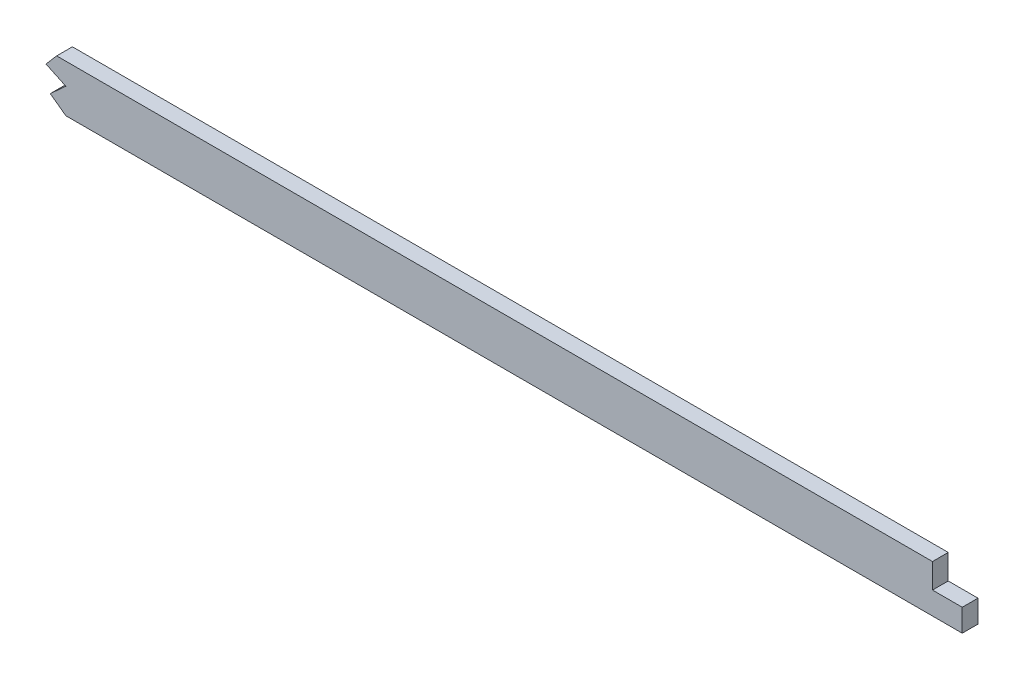
SolidWorks part; units mm, degrees
ref_plane "Front Plane" through (0, 0, 0) normal (0, 0, 1) x (1, 0, 0)
ref_plane "Top Plane" through (0, 0, 0) normal (0, 1, 0) x (1, 0, 0)
ref_plane "Right Plane" through (0, 0, 0) normal (1, 0, 0) x (0, 0, -1)
sketch "Sketch1" plane through (0, 0, 0) normal (0, 0, 1) x (1, 0, 0)
  line L0 (1046.2855, 53.4707) -> (499.61, 53.4707) construction
  line L1 (55, 0) -> (-55, 0) construction
  line L2 (1046.2855, -53.4707) -> (499.61, -53.4707)
  line L3 (1046.2855, -34.4207) -> (499.61, -34.4207)
  line L4 (99.06, -18.1493) -> (99.06, -37.7415)
  line L5 (2669.54, 9.5231) -> (2669.54, -9.569)
  spline S0 degree 5 poles (2699.7923, 7.5245) (2639.6368, 11.6572) (2579.4813, 15.4358) (2518.4981, 19.1485) (2436.3555, 23.2524) (2354.213, 26.6315) (2332.5703, 27.481) (2156.2686, 34.3778) (1979.9669, 41.6286) (1824.1143, 52.7713) (1636.9286, 53.5796) (1449.7429, 53.454) (1418.0067, 53.4707) (1324.8993, 53.4707) (1231.7919, 53.4707) (1170.4413, 53.4707) (1108.7841, 53.4707) (1047.1269, 53.4707) (1046.8464, 53.4707) (1046.5659, 53.4707) (1046.2855, 53.4707) knots 100.654805 100.654805 100.654805 100.654805 100.654805 100.654805 130.927897 130.927897 130.927897 141.337055 141.337055 141.337055 218.101815 218.101815 218.101815 233.772059 233.772059 233.772059 264.077723 264.077723 264.077723 264.216209 264.216209 264.216209 264.216209 264.216209 264.216209 weights 1 1 1 1 1 1 1 1 1 1 1 1 1 1 1 1 1 1 1 1 1 construction
  spline S1 degree 5 poles (499.61, 53.4707) (492.1368, 53.4707) (484.7543, 53.4707) (477.443, 53.4707) (448.5166, 53.4707) (419.5901, 53.4707) (398.3681, 53.4707) (355.6475, 53.4707) (312.927, 53.4707) (289.2351, 53.4703) (265.365, 53.4707) (241.4948, 53.4707) (241.4716, 53.4707) (241.4484, 53.4707) (241.4251, 53.4707) knots 19.90683 19.90683 19.90683 19.90683 19.90683 19.90683 23.637897 23.637897 23.637897 34.276546 34.276546 34.276546 46.401341 46.401341 46.401341 46.413154 46.413154 46.413154 46.413154 46.413154 46.413154 weights 1 1 1 1 1 1 1 1 1 1 1 1 1 1 1 construction
  spline S2 degree 5 poles (241.4251, 53.4707) (224.2869, 53.4707) (207.1495, 53.4673) (190.2039, 52.6866) (151.6561, 49.0319) (113.1083, 41.5037) (91.9499, 36.3426) (71.313, 30.9696) (50.6762, 24.7565) knots 0 0 0 0 0 0 8.713816 8.713816 8.713816 19.90683 19.90683 19.90683 19.90683 19.90683 19.90683 weights 1 1 1 1 1 1 1 1 1 construction
  spline S3 degree 5 poles (241.4251, -53.4707) (224.2869, -53.4707) (207.1495, -53.4673) (190.2039, -52.6866) (151.6561, -49.0319) (113.1083, -41.5037) (91.9499, -36.3426) (71.313, -30.9696) (50.6762, -24.7565) knots 0 0 0 0 0 0 8.713816 8.713816 8.713816 19.90683 19.90683 19.90683 19.90683 19.90683 19.90683 weights 1 1 1 1 1 1 1 1 1
  spline S4 degree 5 poles (499.61, -53.4707) (492.1368, -53.4707) (484.7543, -53.4707) (477.443, -53.4707) (448.5166, -53.4707) (419.5901, -53.4707) (398.3681, -53.4707) (355.6475, -53.4707) (312.927, -53.4707) (289.2351, -53.4703) (265.365, -53.4707) (241.4948, -53.4707) (241.4716, -53.4707) (241.4484, -53.4707) (241.4251, -53.4707) knots 19.90683 19.90683 19.90683 19.90683 19.90683 19.90683 23.637897 23.637897 23.637897 34.276546 34.276546 34.276546 46.401341 46.401341 46.401341 46.413154 46.413154 46.413154 46.413154 46.413154 46.413154 weights 1 1 1 1 1 1 1 1 1 1 1 1 1 1 1
  spline S5 degree 5 poles (2699.7923, -7.5245) (2639.6368, -11.6572) (2579.4813, -15.4358) (2518.4981, -19.1485) (2436.3555, -23.2524) (2354.213, -26.6315) (2332.5703, -27.481) (2156.2686, -34.3778) (1979.9669, -41.6286) (1824.1143, -52.7713) (1636.9286, -53.5796) (1449.7429, -53.454) (1418.0067, -53.4707) (1324.8993, -53.4707) (1231.7919, -53.4707) (1170.4413, -53.4707) (1108.7841, -53.4707) (1047.1269, -53.4707) (1046.8464, -53.4707) (1046.5659, -53.4707) (1046.2855, -53.4707) knots 100.654805 100.654805 100.654805 100.654805 100.654805 100.654805 130.927897 130.927897 130.927897 141.337055 141.337055 141.337055 218.101815 218.101815 218.101815 233.772059 233.772059 233.772059 264.077723 264.077723 264.077723 264.216209 264.216209 264.216209 264.216209 264.216209 264.216209 weights 1 1 1 1 1 1 1 1 1 1 1 1 1 1 1 1 1 1 1 1 1
  spline S6 degree 1 poles (2698.4867, 11.4807) (1046.2855, -34.4207) knots 0 0 1 1 construction
  spline S7 degree 1 poles (499.61, -34.4207) (241.4252, -34.4207) knots 0 0 1 1 construction
  spline S8 degree 1 poles (241.4252, -34.4207) (56.168, -6.5153) knots 0 0 1 1 construction
  spline S9 degree 3 poles (2698.4867, 11.4807) (2691.2474, 10.9833) (2679.1952, 10.1655) (2662.2765, 9.0388) (2635.6663, 7.2925) (2596.8577, 4.8261) (2545.7297, 1.7583) (2494.4053, -1.0986) (2451.533, -3.2666) (2417.1983, -4.8671) (2391.4571, -6.0036) (2365.6347, -7.0869) (2339.5463, -8.1377) (2313.4661, -9.1651) (2287.6124, -10.1795) (2261.7633, -11.201) (2227.2853, -12.5838) (2184.1756, -14.3661) (2132.4291, -16.6074) (2063.4255, -19.7089) (1977.1749, -23.7005) (1873.7325, -28.1494) (1770.3746, -31.6575) (1667.0857, -33.7931) (1581.0111, -34.3832) (1512.074, -34.4278) (1443.0615, -34.4095) (1356.8009, -34.4244) (1218.7946, -34.4185) (1115.289, -34.4207) (1046.2855, -34.4207) knots 100.654805 100.654805 100.654805 100.654805 102.842388 104.300777 105.766098 110.877392 115.988686 121.09998 126.211274 128.766921 131.322568 133.878215 136.433862 138.989509 141.545156 144.100803 146.656449 151.767743 156.879037 161.990331 172.212919 182.435507 192.658094 202.880682 213.10327 218.214564 223.325858 233.548445 243.771033 264.216209 264.216209 264.216209 264.216209
  spline S10 degree 3 poles (499.61, -34.4207) (488.6147, -34.4207) (472.2364, -34.4207) (449.9402, -34.4207) (427.7713, -34.4207) (405.8747, -34.4207) (384.5849, -34.4207) (368.9002, -34.4207) (353.3766, -34.4207) (332.6085, -34.4207) (306.2878, -34.4206) (274.0235, -34.4205) (252.271, -34.4207) (241.4252, -34.4207) knots 19.90683 19.90683 19.90683 19.90683 23.22012 24.876765 26.533411 29.846701 31.503346 33.159992 34.816637 36.473282 39.786573 43.099863 46.413154 46.413154 46.413154 46.413154
  spline S11 degree 3 poles (241.4252, -34.4207) (239.3949, -34.4207) (235.3223, -34.4205) (227.2744, -34.3987) (217.3194, -34.2975) (205.5307, -33.9764) (189.9633, -33.2126) (170.697, -31.5435) (147.5333, -28.3144) (125.4828, -24.2021) (107.4399, -20.1965) (92.2061, -16.4882) (75.9505, -12.2555) (63.6202, -8.7589) (56.168, -6.5153) knots 0 0 0 0 0.622088 1.244177 2.488354 3.732531 4.976707 7.465061 9.953415 12.441768 14.558235 15.802412 17.418476 19.90683 19.90683 19.90683 19.90683
  point P2 (0, 0)
  dimension "D1" = 50.6762
  dimension "D3" = 99.06
  dimension "D4" = 2669.54
  dimension "D2" = 19.05
extrude "Boss-Extrude1" add sketch "Sketch1" along normal mid plane 6.35 contours S10 S11 L4 S3 S4 L2 S5 L5 S9 L3
sketch "Sketch2" plane through (0, 0, 3.175) normal (0, 0, 1) x (1, 0, 0)
  line L0 (2187.01, -14.2633) -> (2312.9875, -14.2633)
  line L1 (2312.9875, -14.2633) -> (2312.9875, -9.1833)
  spline S0 degree 3 poles (689.0175, 232.3189) (4033.8285, 148.9311) (3356.6623, 54.6077) (2635.6663, 7.2925) (2596.8577, 4.8261) (2545.7297, 1.7583) (2494.4053, -1.0986) (2451.533, -3.2666) (2417.1983, -4.8671) (2391.4571, -6.0036) (2365.6347, -7.0869) (2339.5463, -8.1377) (2313.4661, -9.1651) (2287.6124, -10.1795) (2261.7633, -11.201) (2227.2853, -12.5838) (2184.1756, -14.3661) (2132.4291, -16.6074) (2063.4255, -19.7089) (1977.1749, -23.7005) (1873.7325, -28.1494) (1770.3746, -31.6575) (1667.0857, -33.7931) (1581.0111, -34.3832) (1512.074, -34.4278) (1443.0615, -34.4095) (1356.8009, -34.4244) (551.9641, -34.3896) (-218.4198, -34.7282) (-953.6342, -29.9632) knots -106.828462 -106.828462 -106.828462 -106.828462 104.300777 105.766098 110.877392 115.988686 121.09998 126.211274 128.766921 131.322568 133.878215 136.433862 138.989509 141.545156 144.100803 146.656449 151.767743 156.879037 161.990331 172.212919 182.435507 192.658094 202.880682 213.10327 218.214564 223.325858 233.548445 243.771033 461.793666 461.793666 461.793666 461.793666 only from (2669.54, 9.5231) to (1046.2855, -34.4207) construction
  spline S1 degree 3 poles (2669.54, 9.5231) (2667.1265, 9.3624) (2659.8616, 8.8803) (2635.6663, 7.2925) (2596.8577, 4.8261) (2545.7297, 1.7583) (2494.4053, -1.0986) (2451.533, -3.2666) (2417.1983, -4.8671) (2391.4571, -6.0036) (2365.6347, -7.0869) (2339.5463, -8.1377) (2313.4661, -9.1651) (2287.6124, -10.1795) (2261.7633, -11.201) (2227.2853, -12.5838) (2184.1756, -14.3661) (2132.4291, -16.6074) (2063.4255, -19.7089) (1977.1749, -23.7005) (1873.7325, -28.1494) (1770.3746, -31.6575) (1667.0857, -33.7931) (1581.0111, -34.3832) (1512.074, -34.4278) (1443.0615, -34.4095) (1356.8009, -34.4244) (1218.7946, -34.4185) (1115.289, -34.4207) (1046.2855, -34.4207) knots 103.571583 103.571583 103.571583 103.571583 104.300777 105.766098 110.877392 115.988686 121.09998 126.211274 128.766921 131.322568 133.878215 136.433862 138.989509 141.545156 144.100803 146.656449 151.767743 156.879037 161.990331 172.212919 182.435507 192.658094 202.880682 213.10327 218.214564 223.325858 233.548445 243.771033 264.216209 264.216209 264.216209 264.216209
  point P2 (0, 0)
  spline M9 degree 3 poles (2698.4867, 11.4807) (2691.2474, 10.9833) (2679.1952, 10.1655) (2662.2765, 9.0388) (2635.6663, 7.2925) (2596.8577, 4.8261) (2545.7297, 1.7583) (2494.4053, -1.0986) (2451.533, -3.2666) (2417.1983, -4.8671) (2391.4571, -6.0036) (2365.6347, -7.0869) (2339.5463, -8.1377) (2313.4661, -9.1651) (2287.6124, -10.1795) (2261.7633, -11.201) (2227.2853, -12.5838) (2184.1756, -14.3661) (2132.4291, -16.6074) (2063.4255, -19.7089) (1977.1749, -23.7005) (1873.7325, -28.1494) (1770.3746, -31.6575) (1667.0857, -33.7931) (1581.0111, -34.3832) (1512.074, -34.4278) (1443.0615, -34.4095) (1356.8009, -34.4244) (1218.7946, -34.4185) (1115.289, -34.4207) (1046.2855, -34.4207) knots 100.654805 100.654805 100.654805 100.654805 102.842388 104.300777 105.766098 110.877392 115.988686 121.09998 126.211274 128.766921 131.322568 133.878215 136.433862 138.989509 141.545156 144.100803 146.656449 151.767743 156.879037 161.990331 172.212919 182.435507 192.658094 202.880682 213.10327 218.214564 223.325858 233.548445 243.771033 264.216209 264.216209 264.216209 264.216209 only from (2669.54, 9.5231) to (1046.2855, -34.4207)
  dimension "D1" = 2312.9875
  dimension "D2" = 5.08
extrude "Cut-Extrude1" cut sketch "Sketch2" against normal through all contours L0 L1 M9
fillet "Fillet1" radius 2.54 6 edges at (2669.54, -9.569, 0) (2669.54, 9.5231, 0) (99.06, -37.7415, 0) (99.06, -18.1493, 0) (2312.9875, -14.2633, 0)
sketch "Sketch3" plane through (0, 0, 3.175) normal (0, 0, 1) x (1, 0, 0)
  line L15 (1181.434, -34.42) -> (1177.1364, -39.4111)
  line L16 (1177.1364, -39.4111) -> (1185.136, -43.1614)
  line L17 (1185.136, -43.1614) -> (1178.8578, -48.8791)
  line L18 (1178.8578, -48.8791) -> (1185.136, -53.4707)
  line L19 (1534.5209, -34.4089) -> (1534.5209, -44.3802)
  line L20 (1534.5209, -44.3802) -> (1546.518, -44.3802)
  line L21 (1546.518, -44.3802) -> (1546.518, -53.4448)
  line L28 (1181.434, -34.42) -> (1181.434, 141.3554)
  line L29 (1181.434, 141.3554) -> (-115.5761, 193.9941)
  line L30 (-115.5761, 193.9941) -> (0, -269.9706)
  line L31 (0, -269.9706) -> (1185.136, -76.7712)
  line L32 (1185.136, -76.7712) -> (1185.136, -53.4707)
  line L33 (1534.5209, -34.4089) -> (1534.5209, 141.3554)
  line L34 (1534.5209, 141.3554) -> (2732.8108, 122.1822)
  line L35 (2732.8108, 122.1822) -> (2722.6986, -126.981)
  line L36 (2722.6986, -126.981) -> (1547.5069, -59.0647)
  line L37 (1547.5069, -59.0647) -> (1546.518, -53.4448)
  spline S2 degree 3 poles (2187.01, -14.2633) (2186.0643, -14.3032) (2167.8725, -15.0722) (2132.4291, -16.6074) (2063.4255, -19.7089) (1977.1749, -23.7005) (1873.7325, -28.1494) (1770.3746, -31.6575) (1667.0857, -33.7931) (1581.0111, -34.3832) (1512.074, -34.4278) (1443.0615, -34.4095) (1356.8009, -34.4244) (1218.7946, -34.4185) (1115.289, -34.4207) (1046.2855, -34.4207) knots 151.487489 151.487489 151.487489 151.487489 151.767743 156.879037 161.990331 172.212919 182.435507 192.658094 202.880682 213.10327 218.214564 223.325858 233.548445 243.771033 264.216209 264.216209 264.216209 264.216209 construction
  spline S3 degree 5 poles (2667.1682, -9.7266) (2613.4902, -13.2886) (2559.6385, -16.6207) (2505.242, -19.8061) (2429.7275, -23.525) (2354.213, -26.6315) (2332.5703, -27.481) (2156.2686, -34.3778) (1979.9669, -41.6286) (1824.1143, -52.7713) (1636.9286, -53.5796) (1449.7429, -53.454) (1418.0067, -53.4707) (1324.8993, -53.4707) (1231.7919, -53.4707) (1170.4413, -53.4707) (1108.7841, -53.4707) (1047.1269, -53.4707) (1046.8464, -53.4707) (1046.5659, -53.4707) (1046.2855, -53.4707) knots 103.937447 103.937447 103.937447 103.937447 103.937447 103.937447 130.927897 130.927897 130.927897 141.337055 141.337055 141.337055 218.101815 218.101815 218.101815 233.772059 233.772059 233.772059 264.077723 264.077723 264.077723 264.216209 264.216209 264.216209 264.216209 264.216209 264.216209 weights 1 1 1 1 1 1 1 1 1 1 1 1 1 1 1 1 1 1 1 1 1 construction
extrude "Cut-Extrude2" cut sketch "Sketch3" against normal blind 7.62
